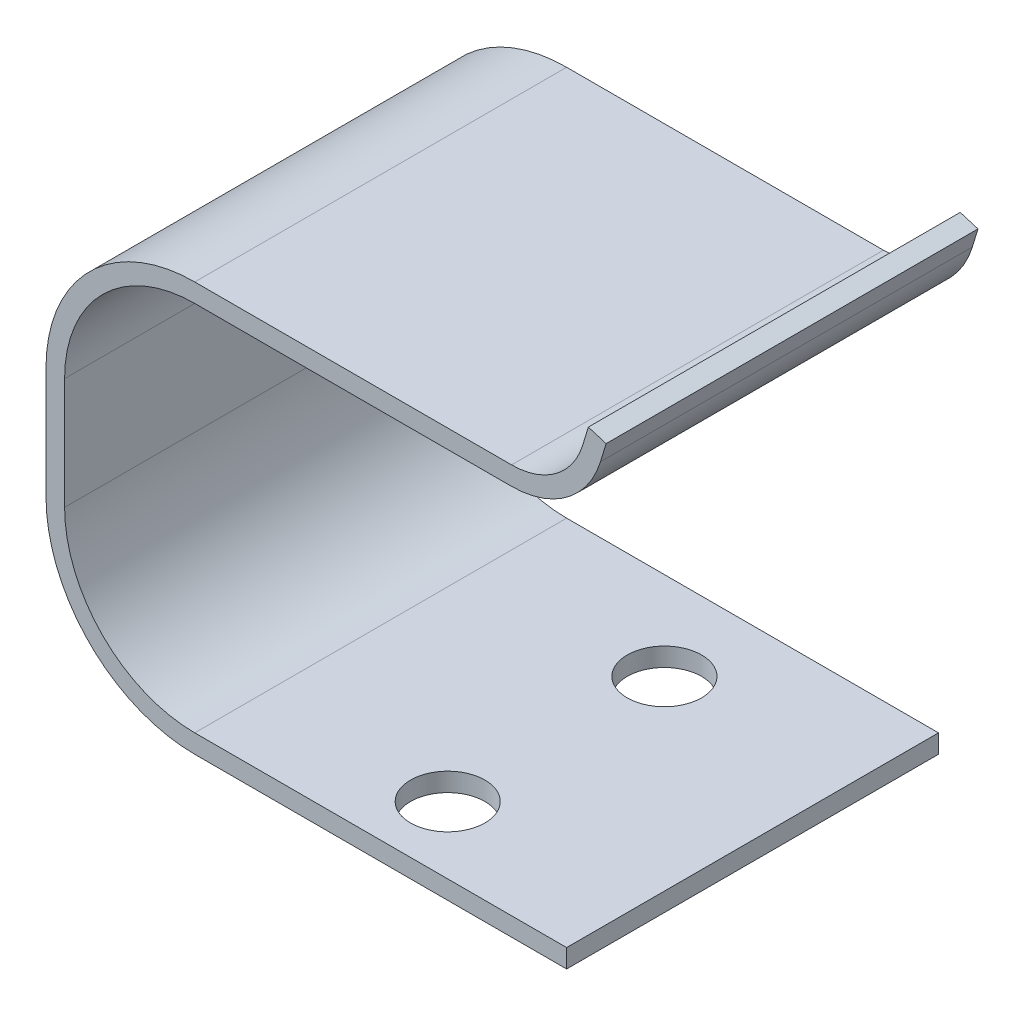
SolidWorks part; units mm, degrees
ref_plane "Plano frontal" through (0, 0, 0) normal (0, 0, 1) x (1, 0, 0)
ref_plane "Plano superior" through (0, 0, 0) normal (0, 1, 0) x (1, 0, 0)
ref_plane "Plano direito" through (0, 0, 0) normal (1, 0, 0) x (0, 0, -1)
sketch "Esboço1" plane through (0, 0, 0) normal (0, 0, 1) x (1, 0, 0)
  line L0 (0, 0) -> (-20, 0)
  line L1 (-28, 8) -> (-28, 14)
  line L2 (-20, 22) -> (-2.9611, 22)
  line L3 (0.8646, 24.8321) -> (1.1679, 25.8257)
  arc A0 (-20, 0) -> (-28, 8) centre (-20, 8) cw
  arc A1 (-28, 14) -> (-20, 22) centre (-20, 14) cw
  arc A2 (0.8646, 24.8321) -> (-2.9611, 22) centre (-2.9611, 26) cw
  dimension "D1" = 8
  dimension "D2" = 4
extrude "Extrusão-Fina1" add sketch "Esboço1" along normal blind 20 thin
sketch "Esboço3" plane through (0, 0, 0) normal (0, -1, 0) x (1, 0, 0)
  circle A0 centre (-10, 16.3954) radius 2
  circle A1 centre (-10, 4.7416) radius 2
extrude "Corte-extrusão1" cut sketch "Esboço3" against normal blind 10
